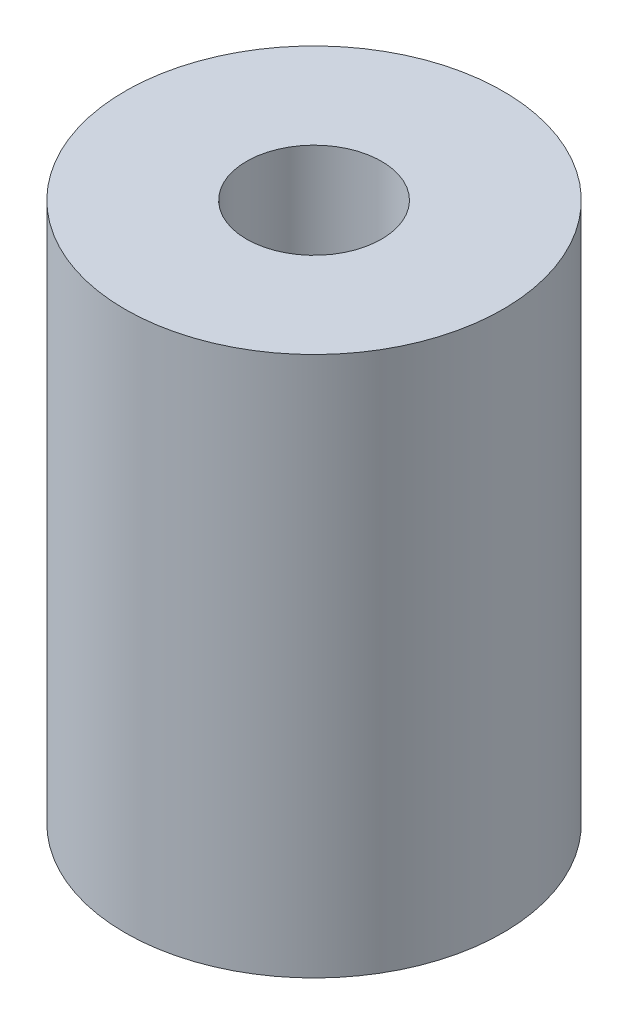
SolidWorks part; units mm, degrees
material "Nylon 101"
ref_plane "Front Plane" through (0, 0, 0) normal (0, 0, 1) x (1, 0, 0)
ref_plane "Top Plane" through (0, 0, 0) normal (0, 1, 0) x (1, 0, 0)
ref_plane "Right Plane" through (0, 0, 0) normal (1, 0, 0) x (0, 0, -1)
sketch "Sketch1" plane through (0, 0, 0) normal (0, 1, 0) x (1, 0, 0)
  circle A0 centre (0, 0) radius 3.5
  circle A1 centre (0, 0) radius 1
  dimension "D1" = 2
  dimension "D2" = 7
extrude "Boss-Extrude1" add sketch "Sketch1" along normal mid plane 10
hole_wizard "M3 Tapped Hole1" positions "Sketch3" profile "Sketch2" tap size "M3" standard "DIN" end condition through all
sketch "Sketch3" plane through (0, 5, 0) normal (0, 1, 0) x (1, 0, 0)
  point P0 (0, 0)
sketch "Sketch2" plane through (0, 5, 0) normal (1, 0, 0) x (0, 0, 1)
  line L0 (0, 0) -> (0, 10)
  line L1 (0, 10) -> (1.25, 10)
  line L2 (1.25, 10) -> (1.25, 0)
  line L5 (1.25, 0) -> (0, 0)
  line L11 (0, -6.35) -> (0, 107.95) construction
  dimension "Thru Tap Drill Dia." = 2.5
  dimension "Thru Tap Drill Depth" = 10
cosmetic thread "Hole Thread1" parameters "D2"=3
